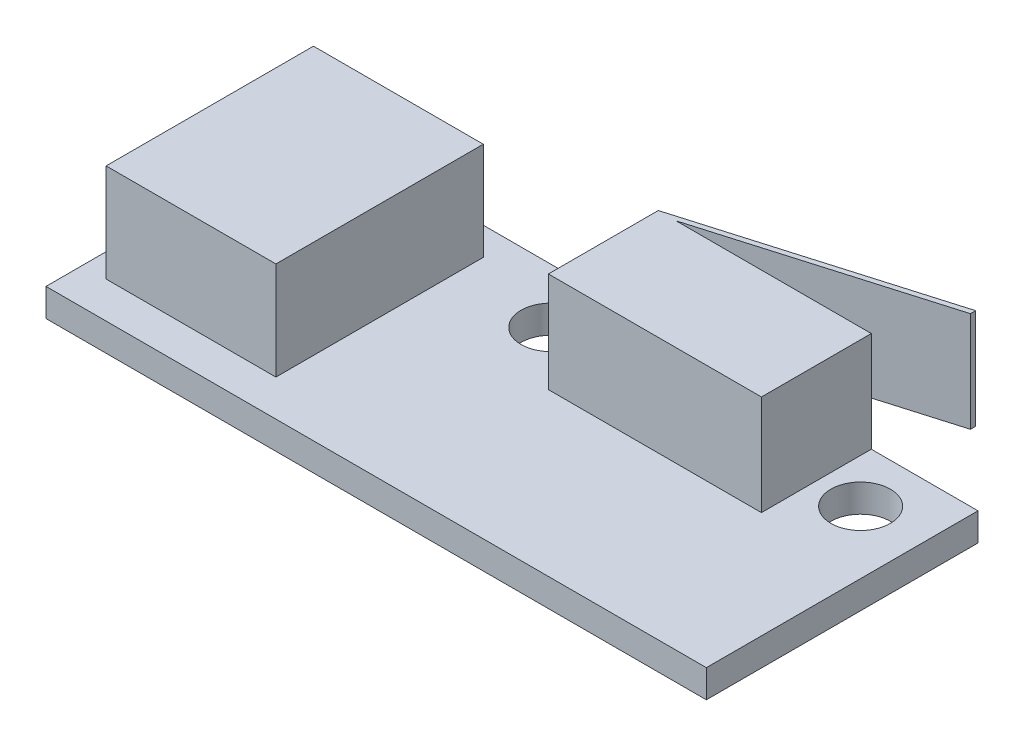
SolidWorks part; units mm, degrees
ref_plane "Front Plane" through (0, 0, 0) normal (0, 0, 1) x (1, 0, 0)
ref_plane "Top Plane" through (0, 0, 0) normal (0, 1, 0) x (1, 0, 0)
ref_plane "Right Plane" through (0, 0, 0) normal (1, 0, 0) x (0, 0, -1)
sketch "Sketch1" plane through (0, 0, 0) normal (0, 1, 0) x (1, 0, 0)
  line L1 (0, 0) -> (-39.55, 0)
  line L2 (0, 0) -> (0, 16.27)
  line L3 (0, 16.27) -> (-39.55, 16.27)
  line L4 (-39.55, 0) -> (-39.55, 16.27)
  point P4 (0, 0)
  dimension "D1" = 39.55
  dimension "D2" = 16.27
extrude "Boss-Extrude1" add sketch "Sketch1" along normal blind 1.67
sketch "Sketch2" plane through (0, 1.67, 0) normal (0, 1, 0) x (1, 0, 0)
  line L0 (0, 16.27) -> (-39.55, 16.27) construction
  line L1 (-19.15, 16.27) -> (-6.39, 16.27)
  line L2 (-19.15, 16.27) -> (-19.15, 9.69)
  line L3 (-19.15, 9.69) -> (-6.39, 9.69)
  line L4 (-6.39, 16.27) -> (-6.39, 9.69)
  line L5 (-19.15, 16.27) -> (-4.45, 20.5826)
  line L6 (-4.45, 20.5826) -> (-4.45, 20.27)
  line L7 (-4.45, 20.27) -> (-18.0843, 16.27)
  line L8 (0, 0) -> (0, 16.27) construction
  point P6 (0, 0)
  point P10 (-7.5878, 20.9245)
  point P11 (-7.6341, 18.424)
  point P12 (-8.0929, 20.4162)
  point P13 (-8.1352, 20.2488)
  line M7 (0, 16.27) -> (-39.55, 16.27)
  dimension "D1" = 0.3
  dimension "D2" = 4
  dimension "D3" = 14.7
  dimension "D4" = 12.76
  dimension "D5" = 6.58
  dimension "D6" = 6.39
extrude "Boss-Extrude2" add sketch "Sketch2" along normal blind 6 contours L7 L6 L5 L1 | L4 L1 L2 L3 M7
sketch "Sketch3" plane through (0, 1.67, 0) normal (0, 1, 0) x (1, 0, 0)
  line L1 (-38.13, 14.6) -> (-27.96, 14.6)
  line L2 (-38.13, 14.6) -> (-38.13, 2.18)
  line L3 (-38.13, 2.18) -> (-27.96, 2.18)
  line L4 (-27.96, 14.6) -> (-27.96, 2.18)
  line L5 (-19.15, 16.27) -> (-39.55, 16.27) construction
  line L6 (-39.55, 16.27) -> (-39.55, 0) construction
  point P4 (-38.2636, 14.3265)
  dimension "D1" = 12.42
  dimension "D2" = 10.17
  dimension "D3" = 1.67
  dimension "D4" = 1.42
extrude "Boss-Extrude3" add sketch "Sketch3" along normal blind 5.87
sketch "Sketch4" plane through (0, 1.67, 0) normal (0, 1, 0) x (1, 0, 0)
  line L0 (0, 0) -> (0, 16.27) construction
  line L1 (0, 16.27) -> (-6.39, 16.27) construction
  circle A0 centre (-22.31, 12.99) radius 1.78
  circle A1 centre (-3.75, 12.99) radius 1.78
  point P4 (0, 0)
  dimension "D1" = 3.56
  dimension "D4" = 3.28
  dimension "D2" = 3.75
  dimension "D3" = 22.31
extrude "Cut-Extrude1" cut sketch "Sketch4" against normal through all
